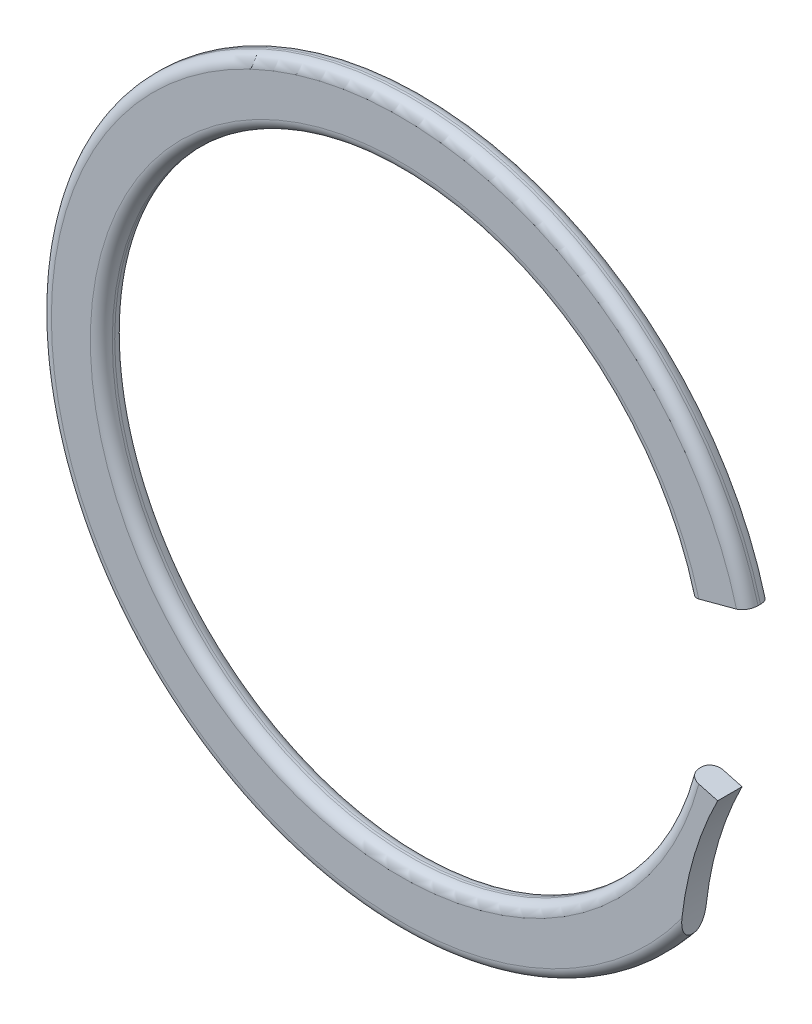
SolidWorks part; units mm, degrees
ref_plane "Front Plane" through (0, 0, 0) normal (0, 0, 1) x (1, 0, 0)
ref_plane "Top Plane" through (0, 0, 0) normal (0, 1, 0) x (1, 0, 0)
ref_plane "Right Plane" through (0, 0, 0) normal (1, 0, 0) x (0, 0, -1)
sketch "Sketch1" plane through (0, 0, 0) normal (0, 0, 1) x (1, 0, 0)
  line L0 (5.6007, 0) -> (6.7437, 0) construction
  line L1 (-5.6007, 0) -> (-6.7437, 0) construction
  line L2 (5.4099, 1.4496) -> (6.5139, 1.7454)
  line L3 (5.4099, -1.4496) -> (6.5139, -1.7454)
  line L4 (5.9619, -1.5975) -> (5.2587, -4.2218) construction
  line L5 (5.2587, -4.2218) -> (4.0275, -3.8919) construction
  line L6 (5.2587, -4.2218) -> (4.3674, -3.5062) construction
  line L7 (4.8131, -3.864) -> (5.9619, -1.5975) construction
  circle A0 centre (0, 0) radius 5.6007
  circle A1 centre (0, 0) radius 6.7437
  arc A3 (5.9619, -1.5975) -> (5.2587, -4.2218) centre (11.8482, -4.5811) ccw
  dimension "Free Diameter" = 13.4874
  dimension "Radial Wall" = 1.143
  dimension "D3" = 30
sketch "Sketch2" plane through (0, 0, 0) normal (0, 0, 1) x (1, 0, 0)
  line L0 (5.4099, -1.4496) -> (6.5139, -1.7454) construction
  line L1 (5.4099, 1.4496) -> (6.5139, 1.7454) construction
  line L2 (5.4099, -1.4496) -> (5.9619, -1.5975)
  line L3 (5.4099, 1.4496) -> (6.5139, 1.7454)
  circle A0 centre (0, 0) radius 6.7437 construction
  circle A2 centre (0, 0) radius 5.6007 construction
  arc A3 (6.5139, 1.7454) -> (5.2587, -4.2218) centre (0, 0) ccw
  arc A4 (5.9619, -1.5975) -> (5.2587, -4.2218) centre (11.8482, -4.5811) ccw construction
  arc A5 (5.4099, 1.4496) -> (5.4099, -1.4496) centre (0, 0) ccw
  arc A6 (5.4099, 1.4496) -> (5.4099, -1.4496) centre (0, 0) cw construction
  arc A7 (6.5139, 1.7454) -> (6.5139, -1.7454) centre (0, 0) cw construction
  arc A8 (5.9619, -1.5975) -> (5.2587, -4.2218) centre (11.8482, -4.5811) ccw
extrude "Extrude1" add sketch "Sketch2" along normal mid plane 0.4572
fillet "Fillet1" radius 0.2057 4 edges at (-6.5993, 1.3882, -0.2286) (-6.5993, 1.3882, 0.2286) (-5.6007, 0, -0.2286) (-5.6007, 0, 0.2286)
sketch "Sketch3" plane through (0, 0, 0) normal (1, 0, 0) x (0, 0, -1)
  line L0 (-0.2794, 6.35) -> (-0.2794, 6.7056)
  line L1 (-0.2794, 6.7056) -> (0.2794, 6.7056)
  line L2 (0.2794, 6.7056) -> (0.2794, 6.35)
  line L3 (0.2794, 6.35) -> (13.8906, 6.35)
  line L5 (-0.2794, 6.35) -> (-1.9844, 6.35)
  line L6 (13.8906, 6.35) -> (13.8906, 7.0612)
  line L7 (-1.9844, 7.0612) -> (-1.9844, 6.35)
  line L8 (-0.2794, 6.7056) -> (-0.2794, 7.0612) construction
  line L9 (-1.9844, 0) -> (13.8906, 0) construction
  line L10 (0, 0) -> (0, 6.7056) construction
  line L11 (13.8906, 7.0612) -> (-1.9844, 7.0612)
  dimension "Groove width" = 0.5588
  dimension "groove dia" = 13.4112
  dimension "shaft dia" = 12.7
  dimension "D4" = 1.9844
  dimension "D1" = 15.875
revolve "Revolve1" [suppressed] add sketch "Sketch3" angle 360 about L9
equation "\"D1@Fillet1\" = (\"Ring Thickness@Extrude1\"*.9)/2"
equation "\"D1@Sketch3\" = \"shaft dia@Sketch3\"*1.25"
equation "\"D4@Sketch3\" = \"D1@Sketch3\"/8"
